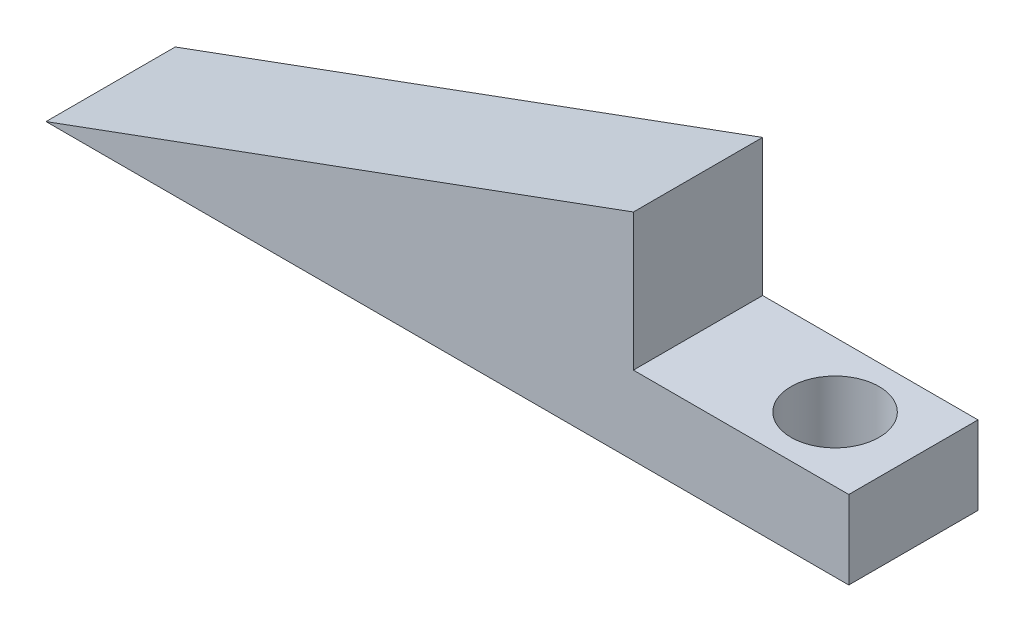
SolidWorks part; units mm, degrees
ref_plane "Front Plane" through (0, 0, 0) normal (0, 0, 1) x (1, 0, 0)
ref_plane "Top Plane" through (0, 0, 0) normal (0, 1, 0) x (1, 0, 0)
ref_plane "Right Plane" through (0, 0, 0) normal (1, 0, 0) x (0, 0, -1)
sketch "Sketch2" plane through (0, 0, 0) normal (0, 0, 1) x (1, 0, 0)
  line L0 (-48.6778, 4.8333) -> (-48.6778, -6.1667)
  line L1 (-48.6778, -6.1667) -> (-78.6778, -6.1667)
  line L2 (-78.6778, -6.1667) -> (-48.6778, 4.8333)
  dimension "D1" = 11
  dimension "D2" = 30
  dimension "D3" = 31.9531
extrude "Boss-Extrude1" add sketch "Sketch2" along normal blind 6.6
sketch "Sketch4" plane through (-48.6778, 0, 0) normal (1, 0, 0) x (0, 0, -1)
  line L0 (0, -6.1667) -> (0, 4.8333) construction
  line L1 (-6.6, -6.1667) -> (0, -6.1667)
  line L2 (-6.6, -6.1667) -> (-6.6, -2.1607)
  line L3 (-6.6, -2.1607) -> (0, -2.1607)
  line L4 (0, -6.1667) -> (0, -2.1607)
extrude "Boss-Extrude2" add sketch "Sketch4" along normal blind 11
hole_wizard "M4 Clearance Hole1" positions "3DSketch1" profile "Sketch5" hole size "M4" standard "ANSI Metric" end condition through all
sketch3d "3DSketch1"
  line L0 (-37.6778, -2.1607, 6.6) -> (-48.6778, -2.1607, 6.6) construction
  line L1 (-37.6778, -2.1607, 0) -> (-37.6778, -2.1607, 6.6) construction
  point P0 (-41.6778, -2.1607, 3.3)
  dimension "D1" = 3.3
  dimension "D2" = 4
sketch "Sketch5" plane through (-41.6778, -2.1607, 3.3) normal (1, 0, 0) x (0, 0, 1)
  line L0 (0, 0) -> (0, 4.0061)
  line L1 (0, 4.0061) -> (2.25, 4.0061)
  line L2 (2.25, 4.0061) -> (2.25, 0)
  line L5 (2.25, 0) -> (0, 0)
  line L11 (0, -6.35) -> (0, 107.95) construction
  dimension "Thru Hole Dia." = 4.5
  dimension "Thru Hole Depth" = 4.0061
